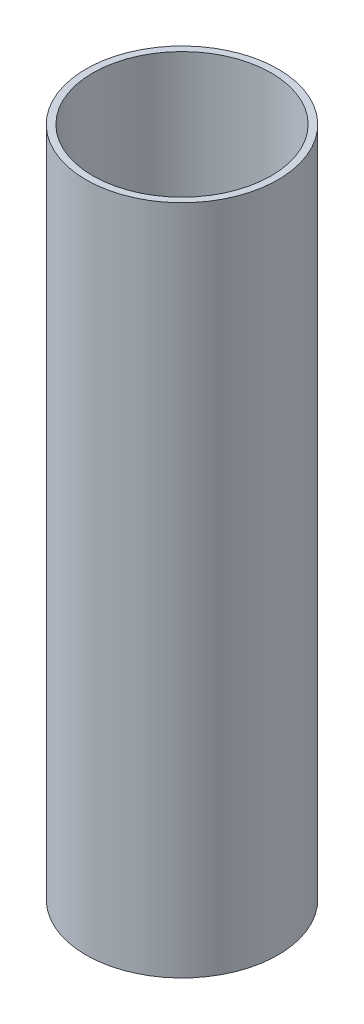
SolidWorks part; units mm, degrees
ref_plane "Front Plane" through (0, 0, 0) normal (0, 0, 1) x (1, 0, 0)
ref_plane "Top Plane" through (0, 0, 0) normal (0, 1, 0) x (1, 0, 0)
ref_plane "Right Plane" through (0, 0, 0) normal (1, 0, 0) x (0, 0, -1)
sketch "Sketch1" plane through (0, 0, 0) normal (0, 0, 1) x (1, 0, 0)
  line L1 (23.622, 0) -> (25.4254, 0)
  line L2 (23.622, 0) -> (23.622, 177.8)
  line L3 (23.622, 177.8) -> (25.4254, 177.8)
  line L4 (25.4254, 0) -> (25.4254, 177.8)
  dimension "D1" = 25.4254
  dimension "D2" = 1.8034
  dimension "D3" = 177.8
  dimension "D4" = 0
ref_axis "Axis1" through (0, -13.97, 0) along (0, 1, 0)
revolve "Revolve1" add sketch "Sketch1" angle 360 about axis through (0, -13.97, 0) along (0, 1, 0)
